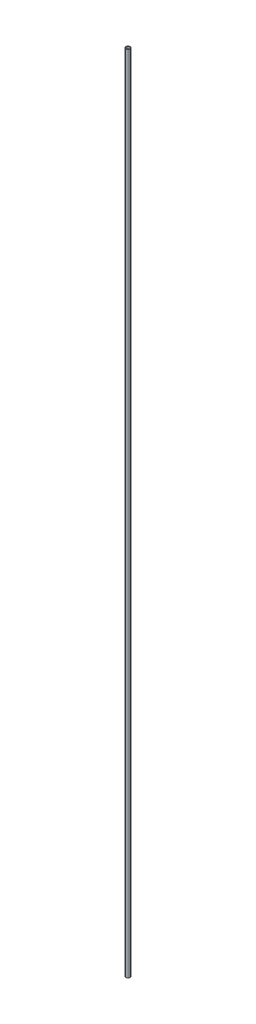
SolidWorks part; units mm, degrees
material "Thornel Mat VMA"
ref_plane "Front Plane" through (0, 0, 0) normal (0, 0, 1) x (1, 0, 0)
ref_plane "Top Plane" through (0, 0, 0) normal (0, 1, 0) x (1, 0, 0)
ref_plane "Right Plane" through (0, 0, 0) normal (1, 0, 0) x (0, 0, -1)
sketch "Sketch1" plane through (0, 0, 0) normal (0, 1, 0) x (1, 0, 0)
  circle A0 centre (0, 0) radius 3.6195
  circle A1 centre (0, 0) radius 2.8575
  dimension "D1" = 7.239
  dimension "D2" = 0.762
extrude "Boss-Extrude1" add sketch "Sketch1" along normal blind 1397
